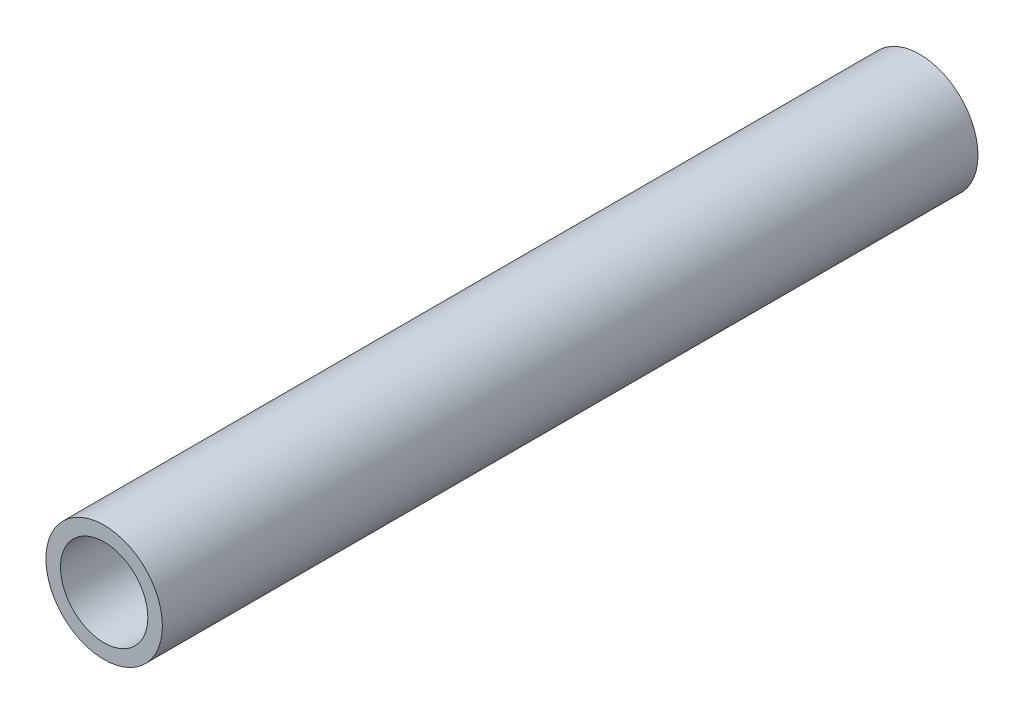
SolidWorks part; units mm, degrees
ref_plane "Front Plane" through (0, 0, 0) normal (0, 0, 1) x (1, 0, 0)
ref_plane "Top Plane" through (0, 0, 0) normal (0, 1, 0) x (1, 0, 0)
ref_plane "Right Plane" through (0, 0, 0) normal (1, 0, 0) x (0, 0, -1)
sketch "Sketch1" plane through (0, 0, 0) normal (0, 0, 1) x (1, 0, 0)
  circle A0 centre (0, 0) radius 12.7
  circle A1 centre (0, 0) radius 9.525
  dimension "D1" = 25.4
  dimension "D2" = 19.05
extrude "Boss-Extrude1" add sketch "Sketch1" along normal blind 177.8
